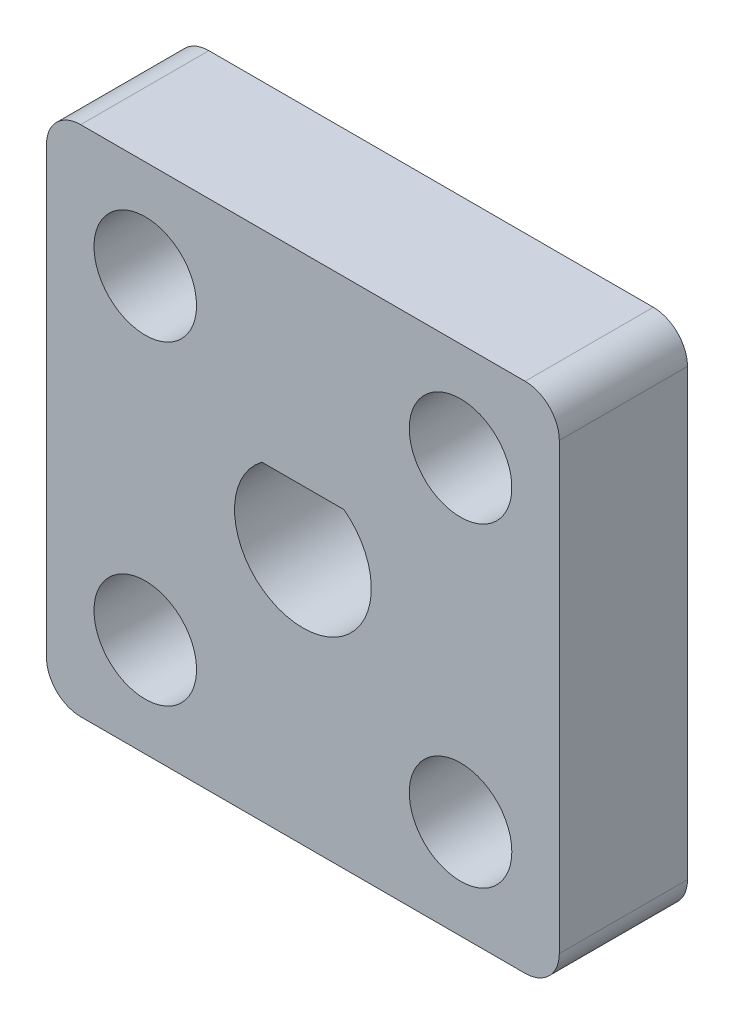
SolidWorks part; units mm, degrees
ref_plane "Front Plane" through (0, 0, 0) normal (0, 0, 1) x (1, 0, 0)
ref_plane "Top Plane" through (0, 0, 0) normal (0, 1, 0) x (1, 0, 0)
ref_plane "Right Plane" through (0, 0, 0) normal (1, 0, 0) x (0, 0, -1)
sketch "Sketch2" plane through (0, 0, 0) normal (0, 0, 1) x (1, 0, 0)
  line L0 (-19.4043, -3.7877) -> (-2.8943, -3.7877)
  line L1 (-20.6743, -2.5177) -> (-20.6743, 13.9923)
  line L2 (-19.4043, 15.2623) -> (-2.8943, 15.2623)
  line L3 (-1.6243, -2.5177) -> (-1.6243, 13.9923)
  line L4 (-20.3024, -3.4157) -> (-1.6243, 15.2623) construction
  line L5 (-20.3024, 14.8904) -> (-1.9963, -3.4157) construction
  line L6 (-11.1493, -3.7877) -> (-11.1493, 15.2623) construction
  line L7 (-20.6743, 5.7373) -> (-1.6243, 5.7373) construction
  line L8 (-17.508, 5.7373) -> (-4.7906, 5.7373) construction
  line L9 (-11.1493, 12.0873) -> (-11.1493, -0.6127) construction
  line L10 (-12.6733, 7.7693) -> (-9.6253, 7.7693)
  circle A0 centre (-17.0057, 11.5937) radius 1.905
  circle A1 centre (-5.293, 11.5937) radius 1.905
  circle A2 centre (-5.293, -0.119) radius 1.905
  circle A3 centre (-17.0057, -0.119) radius 1.905
  arc A4 (-2.8943, 15.2623) -> (-1.6243, 13.9923) centre (-2.8943, 13.9923) cw
  arc A5 (-2.8943, -3.7877) -> (-1.6243, -2.5177) centre (-2.8943, -2.5177) ccw
  arc A6 (-19.4043, -3.7877) -> (-20.6743, -2.5177) centre (-19.4043, -2.5177) cw
  arc A7 (-20.6743, 13.9923) -> (-19.4043, 15.2623) centre (-19.4043, 13.9923) cw
  arc A8 (-12.6733, 7.7693) -> (-9.6253, 7.7693) centre (-11.1493, 5.7373) ccw
  point P0 (-11.1493, 5.7373)
  point P8 (-11.1493, 5.7373)
  point P11 (-11.1493, 5.7373)
  point P40 (-11.1493, 5.7373)
  point P42 (-11.1493, 7.7693)
  dimension "D3" = 1.27
  dimension "D4" = 3.81
  dimension "D5" = 5.08
  dimension "D1" = 19.05
  dimension "D2" = 19.05
  dimension "D6" = 2.032
extrude "Boss-Extrude1" add sketch "Sketch2" along normal blind 4.7625
